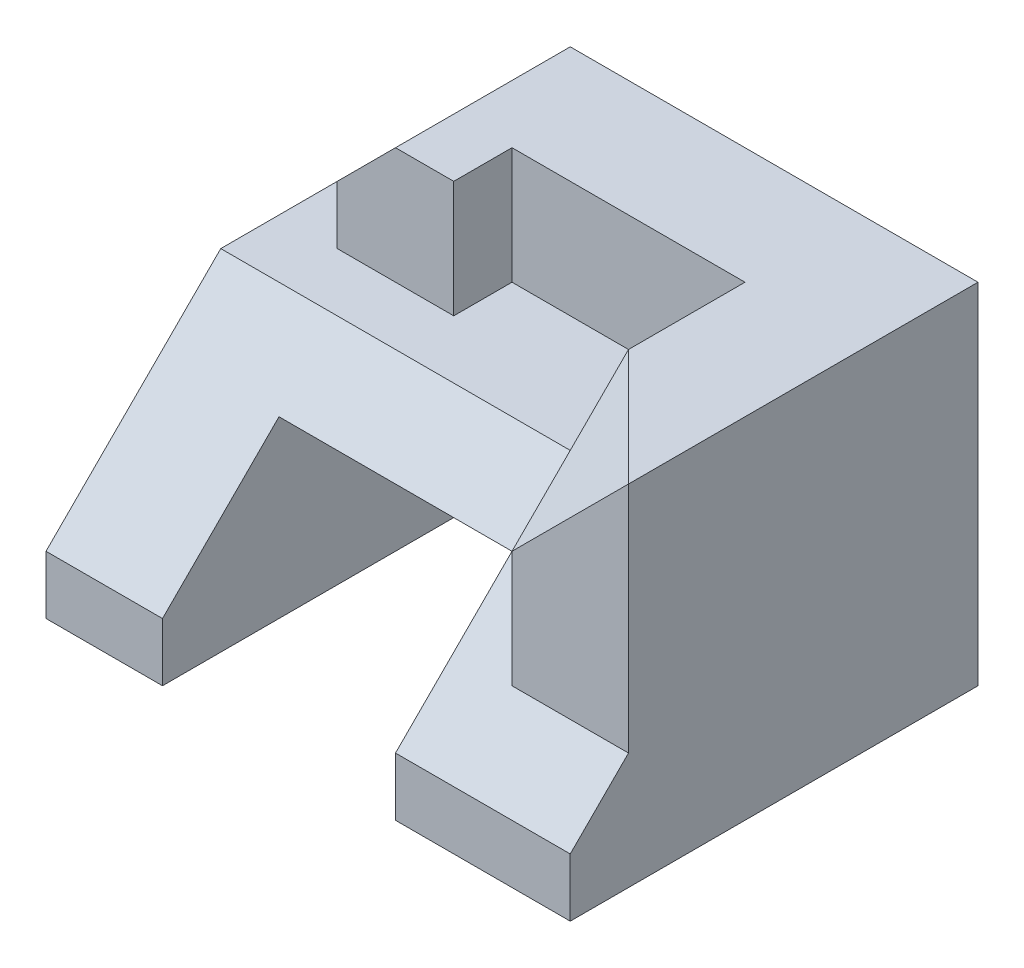
SolidWorks part; units mm, degrees
ref_plane "Front Plane" through (0, 0, 0) normal (0, 0, 1) x (1, 0, 0)
ref_plane "Top Plane" through (0, 0, 0) normal (0, 1, 0) x (1, 0, 0)
ref_plane "Right Plane" through (0, 0, 0) normal (1, 0, 0) x (0, 0, -1)
sketch "Sketch1" plane through (0, 0, 0) normal (0, 0, 1) x (1, 0, 0)
  line L1 (-25, 10) -> (25, 10)
  line L2 (-25, 10) -> (-25, -10)
  line L3 (-25, -10) -> (25, -10)
  line L4 (25, 10) -> (25, -10)
  line L5 (-25, 10) -> (25, -10) construction
  line L6 (-25, -10) -> (25, 10) construction
  point P0 (0, 0)
  dimension "D1" = 50
  dimension "D2" = 20
extrude "Boss-Extrude1" add sketch "Sketch1" along normal blind 30
sketch "Sketch2" plane through (0, 0, 30) normal (0, 0, 1) x (1, 0, 0)
  line L0 (-10, -10) -> (-10, 5)
  line L1 (-25, -10) -> (25, -10) construction
  line L2 (-10, 5) -> (10, 5)
  line L3 (10, 5) -> (10, -10)
  line L4 (10, -10) -> (-10, -10)
  line L5 (-25, 10) -> (-25, -10) construction
  line L6 (25, -10) -> (25, 10) construction
  dimension "D1" = 15
  dimension "D2" = 15
  dimension "D3" = 15
extrude "Cut-Extrude1" cut sketch "Sketch2" against normal through all
sketch "Sketch3" plane through (0, 0, 30) normal (0, 0, 1) x (1, 0, 0)
  line L0 (-25, 10) -> (-20, 10)
  line L1 (25, 10) -> (-25, 10) construction
  line L2 (-20, 10) -> (-20, -10)
  line L3 (-25, -10) -> (-10, -10) construction
  line L4 (-20, -10) -> (-25, -10)
  line L5 (-25, -10) -> (-25, 10)
  dimension "D1" = 5
extrude "Cut-Extrude2" cut sketch "Sketch3" against normal blind 20
sketch "Sketch4" plane through (0, 0, 10) normal (0, 0, 1) x (1, 0, 0)
  line L0 (-20, 10) -> (-25, 0)
  line L1 (-25, 10) -> (-25, -10) construction
  line L2 (-25, 0) -> (-25, 10)
  line L3 (-25, 10) -> (-20, 10)
  dimension "D1" = 10
extrude "Cut-Extrude3" cut sketch "Sketch4" against normal through all
sketch "Sketch5" plane through (-20, 0, 0) normal (-1, 0, 0) x (0, 0, 1)
  line L0 (15, 10) -> (30, -5)
  line L1 (10, 10) -> (30, 10) construction
  line L2 (30, -10) -> (30, 10) construction
  line L3 (30, -5) -> (30, 10)
  line L4 (30, 10) -> (15, 10)
  dimension "D1" = 5
  dimension "D2" = 5
extrude "Cut-Extrude4" cut sketch "Sketch5" against normal through all
sketch "Sketch7" plane through (0, 0, 0) normal (0, 0, -1) x (-1, 0, 0)
  line L0 (-25, -10) -> (-25, 20)
  line L1 (-25, 20) -> (15, 20)
  line L2 (15, 20) -> (15, -10)
  line L3 (25, -10) -> (10, -10) construction
  line L4 (15, -10) -> (-25, -10)
  dimension "D1" = 5
  dimension "D2" = 30
extrude "Boss-Extrude2" add sketch "Sketch7" along normal blind 5
sketch "Sketch8" plane through (0, 0, 0) normal (0, 0, 1) x (1, 0, 0)
  line L0 (-10, 5) -> (10, 5)
  line L1 (10, 5) -> (10, -10)
  line L2 (10, -10) -> (-10, -10)
  line L3 (-10, -10) -> (-10, 5)
extrude "Cut-Extrude5" cut sketch "Sketch8" against normal through all
sketch "Sketch9" plane through (0, 10, 0) normal (0, 1, 0) x (1, 0, 0)
  line L0 (-15, 0) -> (-15, -10)
  line L1 (-15, -10) -> (25, -10)
  line L2 (25, -15) -> (25, 0) construction
  line L3 (25, -10) -> (25, 0)
  line L4 (-15, 0) -> (25, 0)
  dimension "D1" = 10
extrude "Boss-Extrude3" add sketch "Sketch9" along normal blind 10
sketch "Sketch10" plane through (0, 0, 10) normal (0, 0, 1) x (1, 0, 0)
  line L0 (-5, 10) -> (-5, 20)
  line L1 (-15, 10) -> (25, 10) construction
  line L2 (-15, 20) -> (25, 20) construction
  line L3 (-5, 20) -> (15, 20)
  line L4 (15, 20) -> (15, 10)
  line L5 (15, 10) -> (-5, 10)
  line L6 (-15, 20) -> (-15, 10) construction
  line L7 (25, 20) -> (25, 10) construction
  dimension "D1" = 10
  dimension "D2" = 10
extrude "Cut-Extrude6" cut sketch "Sketch10" against normal blind 5
sketch "Sketch11" plane through (0, 0, 10) normal (0, 0, 1) x (1, 0, 0)
  line L0 (-15, 20) -> (-10, 20)
  line L1 (-15, 20) -> (-5, 20) construction
  line L2 (-10, 20) -> (-15, 15)
  line L3 (-15, 20) -> (-15, 10) construction
  line L4 (-15, 15) -> (-15, 20)
  dimension "D1" = 5
  dimension "D2" = 5
extrude "Cut-Extrude7" cut sketch "Sketch11" against normal through all
sketch "Sketch12" plane through (0, 0, 10) normal (0, 0, 1) x (1, 0, 0)
  line L0 (15, 20) -> (25, 20)
  line L1 (25, 20) -> (25, 10)
  line L2 (25, 10) -> (15, 10)
  line L3 (15, 10) -> (15, 20)
extrude "Boss-Extrude4" add sketch "Sketch12" along normal blind 5
sketch "Sketch13" plane through (0, 0, 15) normal (0, 0, 1) x (1, 0, 0)
  line L0 (15, 20) -> (25, 20)
  line L1 (25, 20) -> (25, 10)
  line L2 (25, 10) -> (15, 10)
  line L3 (15, 10) -> (15, 20)
extrude "Boss-Extrude5" add sketch "Sketch13" along normal blind 10
sketch "Sketch14" plane through (0, 10, 0) normal (0, -1, 0) x (1, 0, 0)
  line L0 (25, 25) -> (15, 25)
  line L1 (15, 25) -> (25, 25) construction
  line L2 (15, 25) -> (15, 15)
  line L3 (15, 15) -> (25, 15)
  line L4 (25, 15) -> (25, 25)
extrude "Boss-Extrude6" add sketch "Sketch14" along normal blind 10
sketch "Sketch15" plane through (0, 20, 0) normal (0, 1, 0) x (1, 0, 0)
  line L0 (15, -5) -> (15, -25) construction
  point P0 (15, -15)
  dimension "D1" = 10
sketch "Sketch16" plane through (0, 0, 25) normal (0, 0, 1) x (1, 0, 0)
  line L0 (15, 20) -> (15, 0) construction
  point P0 (15, 10)
  dimension "D1" = 10
ref_plane "Plane1" through (-6.6667, 6.6667, 6.6667) normal (-0.5774, 0.5774, 0.5774) x (0.8165, 0.4082, 0.4082)
sketch "Sketch17" plane through (-6.6667, 6.6667, 6.6667) normal (-0.5774, 0.5774, 0.5774) x (0.8165, 0.4082, 0.4082)
  line L0 (26.5361, 3.5355) -> (38.7836, -3.5355)
  line L1 (38.7836, -3.5355) -> (26.5361, -10.6066)
  line L2 (26.5361, -10.6066) -> (26.5361, 3.5355)
extrude "Cut-Extrude8" cut sketch "Sketch17" along normal blind 10
